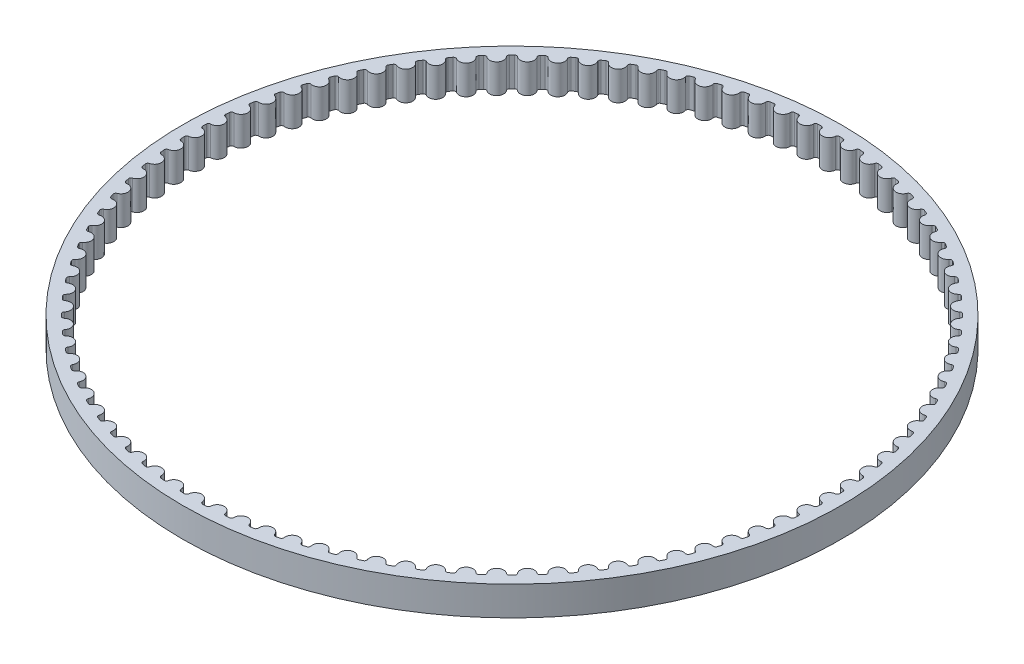
SolidWorks part; units mm, degrees
ref_plane "Front Plane" through (0, 0, 0) normal (0, 0, 1) x (1, 0, 0)
ref_plane "Top Plane" through (0, 0, 0) normal (0, 1, 0) x (1, 0, 0)
ref_plane "Right Plane" through (0, 0, 0) normal (1, 0, 0) x (0, 0, -1)
sketch "Sketch1" plane through (0, 0, 0) normal (0, 1, 0) x (1, 0, 0)
  circle A0 centre (0, 0) radius 45.0458
  arc B0 (-1.7256, -43.5116) -> (-1.2478, -43.5279) centre (0, 0) ccw
  arc B1 (-1.2478, -43.5279) -> (-0.9418, -43.2593) centre (-1.2392, -43.229) ccw
  arc B2 (0.9418, -43.2593) -> (-0.9418, -43.2593) centre (0, -43.3553) ccw
  arc B3 (0.9418, -43.2593) -> (1.2478, -43.5279) centre (1.2392, -43.229) ccw
  arc B4 (1.2478, -43.5279) -> (1.7256, -43.5116) centre (0, 0) ccw
  arc B5 (1.7256, -43.5116) -> (2.0125, -43.2227) centre (1.7137, -43.2128) ccw
  arc B6 (3.8917, -43.0942) -> (2.0125, -43.2227) centre (2.9587, -43.2542) ccw
  arc B7 (3.8917, -43.0942) -> (4.2153, -43.3413) centre (4.1864, -43.0437) ccw
  arc B8 (4.2153, -43.3413) -> (4.6909, -43.2924) centre (0, 0) ccw
  arc B9 (4.6909, -43.2924) -> (4.9575, -42.9846) centre (4.6587, -42.9951) ccw
  arc B10 (6.8235, -42.7282) -> (4.9575, -42.9846) centre (5.9035, -42.9515) ccw
  arc B11 (6.8235, -42.7282) -> (7.1632, -42.9526) centre (7.114, -42.6576) ccw
  arc B12 (7.1632, -42.9526) -> (7.6343, -42.8713) centre (0, 0) ccw
  arc B13 (7.6343, -42.8713) -> (7.8793, -42.5461) centre (7.5819, -42.577) ccw
  arc B14 (9.7234, -42.1629) -> (7.8793, -42.5461) centre (8.8209, -42.4484) ccw
  arc B15 (9.7234, -42.1629) -> (10.0777, -42.3636) centre (10.0085, -42.0727) ccw
  arc B16 (10.0777, -42.3636) -> (10.5422, -42.2504) centre (0, 0) ccw
  arc B17 (10.5422, -42.2504) -> (10.7644, -41.9092) centre (10.4698, -41.9603) ccw
  arc B18 (12.5781, -41.4011) -> (10.7644, -41.9092) centre (11.6971, -41.7475) ccw
  arc B19 (12.5781, -41.4011) -> (12.9452, -41.5771) centre (12.8563, -41.2916) ccw
  arc B20 (12.9452, -41.5771) -> (13.4008, -41.4325) centre (0, 0) ccw
  arc B21 (13.4008, -41.4325) -> (13.5993, -41.0769) centre (13.3088, -41.148) ccw
  arc B22 (15.3741, -40.4462) -> (13.5993, -41.0769) centre (14.5188, -40.852) ccw
  arc B23 (15.3741, -40.4462) -> (15.7524, -40.5968) centre (15.6442, -40.318) ccw
  arc B24 (15.7524, -40.5968) -> (16.1971, -40.4214) centre (0, 0) ccw
  arc B25 (16.1971, -40.4214) -> (16.3708, -40.0531) centre (16.0858, -40.1438) ccw
  arc B26 (18.0984, -39.3027) -> (16.3708, -40.0531) centre (17.2728, -39.7659) ccw
  arc B27 (18.0984, -39.3027) -> (18.4861, -39.4271) centre (18.3591, -39.1564) ccw
  arc B28 (18.4861, -39.4271) -> (18.9178, -39.2218) centre (0, 0) ccw
  arc B29 (18.9178, -39.2218) -> (19.0659, -38.8426) centre (18.7879, -38.9525) ccw
  arc B30 (20.7383, -37.976) -> (19.0659, -38.8426) centre (19.9462, -38.4945) ccw
  arc B31 (20.7383, -37.976) -> (21.1336, -38.0737) centre (20.9884, -37.8123) ccw
  arc B32 (21.1336, -38.0737) -> (21.5502, -37.8394) centre (0, 0) ccw
  arc B33 (21.5502, -37.8394) -> (21.6722, -37.4509) centre (21.4023, -37.5796) ccw
  arc B34 (23.2815, -36.4723) -> (21.6722, -37.4509) centre (22.5267, -37.0436) ccw
  arc B35 (23.2815, -36.4723) -> (23.6825, -36.5427) centre (23.5199, -36.2918) ccw
  arc B36 (23.6825, -36.5427) -> (24.0823, -36.2806) centre (0, 0) ccw
  arc B37 (24.0823, -36.2806) -> (24.1774, -35.8847) centre (23.9169, -36.0314) ccw
  arc B38 (25.7162, -34.7985) -> (24.1774, -35.8847) centre (25.0021, -35.4199) ccw
  arc B39 (25.7162, -34.7985) -> (26.1211, -34.8414) centre (25.9417, -34.6022) ccw
  arc B40 (26.1211, -34.8414) -> (26.502, -34.5525) centre (0, 0) ccw
  arc B41 (26.502, -34.5525) -> (26.5699, -34.1511) centre (26.32, -34.3153) ccw
  arc B42 (28.031, -32.9624) -> (26.5699, -34.1511) centre (27.361, -33.6312) ccw
  arc B43 (28.031, -32.9624) -> (28.4379, -32.9776) centre (28.2426, -32.7512) ccw
  arc B44 (28.4379, -32.9776) -> (28.7982, -32.6634) centre (0, 0) ccw
  arc B45 (28.7982, -32.6634) -> (28.8385, -32.2583) centre (28.6004, -32.4392) ccw
  arc B46 (30.2151, -30.9727) -> (28.8385, -32.2583) centre (29.5923, -31.6856) ccw
  arc B47 (30.2151, -30.9727) -> (30.622, -30.9601) centre (30.4118, -30.7475) ccw
  arc B48 (30.622, -30.9601) -> (30.9601, -30.622) centre (0, 0) ccw
  arc B49 (30.9601, -30.622) -> (30.9727, -30.2151) centre (30.7475, -30.4118) ccw
  arc B50 (32.2583, -28.8385) -> (30.9727, -30.2151) centre (31.6856, -29.5923) ccw
  arc B51 (32.2583, -28.8385) -> (32.6634, -28.7982) centre (32.4392, -28.6004) ccw
  arc B52 (32.6634, -28.7982) -> (32.9776, -28.4379) centre (0, 0) ccw
  arc B53 (32.9776, -28.4379) -> (32.9624, -28.031) centre (32.7512, -28.2426) ccw
  arc B54 (34.1511, -26.5699) -> (32.9624, -28.031) centre (33.6312, -27.361) ccw
  arc B55 (34.1511, -26.5699) -> (34.5525, -26.502) centre (34.3153, -26.32) ccw
  arc B56 (34.5525, -26.502) -> (34.8414, -26.1211) centre (0, 0) ccw
  arc B57 (34.8414, -26.1211) -> (34.7985, -25.7162) centre (34.6022, -25.9417) ccw
  arc B58 (35.8847, -24.1774) -> (34.7985, -25.7162) centre (35.4199, -25.0021) ccw
  arc B59 (35.8847, -24.1774) -> (36.2806, -24.0823) centre (36.0314, -23.9169) ccw
  arc B60 (36.2806, -24.0823) -> (36.5427, -23.6825) centre (0, 0) ccw
  arc B61 (36.5427, -23.6825) -> (36.4723, -23.2815) centre (36.2918, -23.5199) ccw
  arc B62 (37.4509, -21.6722) -> (36.4723, -23.2815) centre (37.0436, -22.5267) ccw
  arc B63 (37.4509, -21.6722) -> (37.8394, -21.5502) centre (37.5796, -21.4023) ccw
  arc B64 (37.8394, -21.5502) -> (38.0737, -21.1336) centre (0, 0) ccw
  arc B65 (38.0737, -21.1336) -> (37.976, -20.7383) centre (37.8123, -20.9884) ccw
  arc B66 (38.8426, -19.0659) -> (37.976, -20.7383) centre (38.4945, -19.9462) ccw
  arc B67 (38.8426, -19.0659) -> (39.2218, -18.9178) centre (38.9525, -18.7879) ccw
  arc B68 (39.2218, -18.9178) -> (39.4271, -18.4861) centre (0, 0) ccw
  arc B69 (39.4271, -18.4861) -> (39.3027, -18.0984) centre (39.1564, -18.3591) ccw
  arc B70 (40.0531, -16.3708) -> (39.3027, -18.0984) centre (39.7659, -17.2728) ccw
  arc B71 (40.0531, -16.3708) -> (40.4214, -16.1971) centre (40.1438, -16.0858) ccw
  arc B72 (40.4214, -16.1971) -> (40.5968, -15.7524) centre (0, 0) ccw
  arc B73 (40.5968, -15.7524) -> (40.4462, -15.3741) centre (40.318, -15.6442) ccw
  arc B74 (41.0769, -13.5993) -> (40.4462, -15.3741) centre (40.852, -14.5188) ccw
  arc B75 (41.0769, -13.5993) -> (41.4325, -13.4008) centre (41.148, -13.3088) ccw
  arc B76 (41.4325, -13.4008) -> (41.5771, -12.9452) centre (0, 0) ccw
  arc B77 (41.5771, -12.9452) -> (41.4011, -12.5781) centre (41.2916, -12.8563) ccw
  arc B78 (41.9092, -10.7644) -> (41.4011, -12.5781) centre (41.7475, -11.6971) ccw
  arc B79 (41.9092, -10.7644) -> (42.2504, -10.5422) centre (41.9603, -10.4698) ccw
  arc B80 (42.2504, -10.5422) -> (42.3636, -10.0777) centre (0, 0) ccw
  arc B81 (42.3636, -10.0777) -> (42.1629, -9.7234) centre (42.0727, -10.0085) ccw
  arc B82 (42.5461, -7.8793) -> (42.1629, -9.7234) centre (42.4484, -8.8209) ccw
  arc B83 (42.5461, -7.8793) -> (42.8713, -7.6343) centre (42.577, -7.5819) ccw
  arc B84 (42.8713, -7.6343) -> (42.9526, -7.1632) centre (0, 0) ccw
  arc B85 (42.9526, -7.1632) -> (42.7282, -6.8235) centre (42.6576, -7.114) ccw
  arc B86 (42.9846, -4.9575) -> (42.7282, -6.8235) centre (42.9515, -5.9035) ccw
  arc B87 (42.9846, -4.9575) -> (43.2924, -4.6909) centre (42.9951, -4.6587) ccw
  arc B88 (43.2924, -4.6909) -> (43.3413, -4.2153) centre (0, 0) ccw
  arc B89 (43.3413, -4.2153) -> (43.0942, -3.8917) centre (43.0437, -4.1864) ccw
  arc B90 (43.2227, -2.0125) -> (43.0942, -3.8917) centre (43.2542, -2.9587) ccw
  arc B91 (43.2227, -2.0125) -> (43.5116, -1.7256) centre (43.2128, -1.7137) ccw
  arc B92 (43.5116, -1.7256) -> (43.5279, -1.2478) centre (0, 0) ccw
  arc B93 (43.5279, -1.2478) -> (43.2593, -0.9418) centre (43.229, -1.2392) ccw
  arc B94 (43.2593, 0.9418) -> (43.2593, -0.9418) centre (43.3553, 0) ccw
  arc B95 (43.2593, 0.9418) -> (43.5279, 1.2478) centre (43.229, 1.2392) ccw
  arc B96 (43.5279, 1.2478) -> (43.5116, 1.7256) centre (0, 0) ccw
  arc B97 (43.5116, 1.7256) -> (43.2227, 2.0125) centre (43.2128, 1.7137) ccw
  arc B98 (43.0942, 3.8917) -> (43.2227, 2.0125) centre (43.2542, 2.9587) ccw
  arc B99 (43.0942, 3.8917) -> (43.3413, 4.2153) centre (43.0437, 4.1864) ccw
  arc B100 (43.3413, 4.2153) -> (43.2924, 4.6909) centre (0, 0) ccw
  arc B101 (43.2924, 4.6909) -> (42.9846, 4.9575) centre (42.9951, 4.6587) ccw
  arc B102 (42.7282, 6.8235) -> (42.9846, 4.9575) centre (42.9515, 5.9035) ccw
  arc B103 (42.7282, 6.8235) -> (42.9526, 7.1632) centre (42.6576, 7.114) ccw
  arc B104 (42.9526, 7.1632) -> (42.8713, 7.6343) centre (0, 0) ccw
  arc B105 (42.8713, 7.6343) -> (42.5461, 7.8793) centre (42.577, 7.5819) ccw
  arc B106 (42.1629, 9.7234) -> (42.5461, 7.8793) centre (42.4484, 8.8209) ccw
  arc B107 (42.1629, 9.7234) -> (42.3636, 10.0777) centre (42.0727, 10.0085) ccw
  arc B108 (42.3636, 10.0777) -> (42.2504, 10.5422) centre (0, 0) ccw
  arc B109 (42.2504, 10.5422) -> (41.9092, 10.7644) centre (41.9603, 10.4698) ccw
  arc B110 (41.4011, 12.5781) -> (41.9092, 10.7644) centre (41.7475, 11.6971) ccw
  arc B111 (41.4011, 12.5781) -> (41.5771, 12.9452) centre (41.2916, 12.8563) ccw
  arc B112 (41.5771, 12.9452) -> (41.4325, 13.4008) centre (0, 0) ccw
  arc B113 (41.4325, 13.4008) -> (41.0769, 13.5993) centre (41.148, 13.3088) ccw
  arc B114 (40.4462, 15.3741) -> (41.0769, 13.5993) centre (40.852, 14.5188) ccw
  arc B115 (40.4462, 15.3741) -> (40.5968, 15.7524) centre (40.318, 15.6442) ccw
  arc B116 (40.5968, 15.7524) -> (40.4214, 16.1971) centre (0, 0) ccw
  arc B117 (40.4214, 16.1971) -> (40.0531, 16.3708) centre (40.1438, 16.0858) ccw
  arc B118 (39.3027, 18.0984) -> (40.0531, 16.3708) centre (39.7659, 17.2728) ccw
  arc B119 (39.3027, 18.0984) -> (39.4271, 18.4861) centre (39.1564, 18.3591) ccw
  arc B120 (39.4271, 18.4861) -> (39.2218, 18.9178) centre (0, 0) ccw
  arc B121 (39.2218, 18.9178) -> (38.8426, 19.0659) centre (38.9525, 18.7879) ccw
  arc B122 (37.976, 20.7383) -> (38.8426, 19.0659) centre (38.4945, 19.9462) ccw
  arc B123 (37.976, 20.7383) -> (38.0737, 21.1336) centre (37.8123, 20.9884) ccw
  arc B124 (38.0737, 21.1336) -> (37.8394, 21.5502) centre (0, 0) ccw
  arc B125 (37.8394, 21.5502) -> (37.4509, 21.6722) centre (37.5796, 21.4023) ccw
  arc B126 (36.4723, 23.2815) -> (37.4509, 21.6722) centre (37.0436, 22.5267) ccw
  arc B127 (36.4723, 23.2815) -> (36.5427, 23.6825) centre (36.2918, 23.5199) ccw
  arc B128 (36.5427, 23.6825) -> (36.2806, 24.0823) centre (0, 0) ccw
  arc B129 (36.2806, 24.0823) -> (35.8847, 24.1774) centre (36.0314, 23.9169) ccw
  arc B130 (34.7985, 25.7162) -> (35.8847, 24.1774) centre (35.4199, 25.0021) ccw
  arc B131 (34.7985, 25.7162) -> (34.8414, 26.1211) centre (34.6022, 25.9417) ccw
  arc B132 (34.8414, 26.1211) -> (34.5525, 26.502) centre (0, 0) ccw
  arc B133 (34.5525, 26.502) -> (34.1511, 26.5699) centre (34.3153, 26.32) ccw
  arc B134 (32.9624, 28.031) -> (34.1511, 26.5699) centre (33.6312, 27.361) ccw
  arc B135 (32.9624, 28.031) -> (32.9776, 28.4379) centre (32.7512, 28.2426) ccw
  arc B136 (32.9776, 28.4379) -> (32.6634, 28.7982) centre (0, 0) ccw
  arc B137 (32.6634, 28.7982) -> (32.2583, 28.8385) centre (32.4392, 28.6004) ccw
  arc B138 (30.9727, 30.2151) -> (32.2583, 28.8385) centre (31.6856, 29.5923) ccw
  arc B139 (30.9727, 30.2151) -> (30.9601, 30.622) centre (30.7475, 30.4118) ccw
  arc B140 (30.9601, 30.622) -> (30.622, 30.9601) centre (0, 0) ccw
  arc B141 (30.622, 30.9601) -> (30.2151, 30.9727) centre (30.4118, 30.7475) ccw
  arc B142 (28.8385, 32.2583) -> (30.2151, 30.9727) centre (29.5923, 31.6856) ccw
  arc B143 (28.8385, 32.2583) -> (28.7982, 32.6634) centre (28.6004, 32.4392) ccw
  arc B144 (28.7982, 32.6634) -> (28.4379, 32.9776) centre (0, 0) ccw
  arc B145 (28.4379, 32.9776) -> (28.031, 32.9624) centre (28.2426, 32.7512) ccw
  arc B146 (26.5699, 34.1511) -> (28.031, 32.9624) centre (27.361, 33.6312) ccw
  arc B147 (26.5699, 34.1511) -> (26.502, 34.5525) centre (26.32, 34.3153) ccw
  arc B148 (26.502, 34.5525) -> (26.1211, 34.8414) centre (0, 0) ccw
  arc B149 (26.1211, 34.8414) -> (25.7162, 34.7985) centre (25.9417, 34.6022) ccw
  arc B150 (24.1774, 35.8847) -> (25.7162, 34.7985) centre (25.0021, 35.4199) ccw
  arc B151 (24.1774, 35.8847) -> (24.0823, 36.2806) centre (23.9169, 36.0314) ccw
  arc B152 (24.0823, 36.2806) -> (23.6825, 36.5427) centre (0, 0) ccw
  arc B153 (23.6825, 36.5427) -> (23.2815, 36.4723) centre (23.5199, 36.2918) ccw
  arc B154 (21.6722, 37.4509) -> (23.2815, 36.4723) centre (22.5267, 37.0436) ccw
  arc B155 (21.6722, 37.4509) -> (21.5502, 37.8394) centre (21.4023, 37.5796) ccw
  arc B156 (21.5502, 37.8394) -> (21.1336, 38.0737) centre (0, 0) ccw
  arc B157 (21.1336, 38.0737) -> (20.7383, 37.976) centre (20.9884, 37.8123) ccw
  arc B158 (19.0659, 38.8426) -> (20.7383, 37.976) centre (19.9462, 38.4945) ccw
  arc B159 (19.0659, 38.8426) -> (18.9178, 39.2218) centre (18.7879, 38.9525) ccw
  arc B160 (18.9178, 39.2218) -> (18.4861, 39.4271) centre (0, 0) ccw
  arc B161 (18.4861, 39.4271) -> (18.0984, 39.3027) centre (18.3591, 39.1564) ccw
  arc B162 (16.3708, 40.0531) -> (18.0984, 39.3027) centre (17.2728, 39.7659) ccw
  arc B163 (16.3708, 40.0531) -> (16.1971, 40.4214) centre (16.0858, 40.1438) ccw
  arc B164 (16.1971, 40.4214) -> (15.7524, 40.5968) centre (0, 0) ccw
  arc B165 (15.7524, 40.5968) -> (15.3741, 40.4462) centre (15.6442, 40.318) ccw
  arc B166 (13.5993, 41.0769) -> (15.3741, 40.4462) centre (14.5188, 40.852) ccw
  arc B167 (13.5993, 41.0769) -> (13.4008, 41.4325) centre (13.3088, 41.148) ccw
  arc B168 (13.4008, 41.4325) -> (12.9452, 41.5771) centre (0, 0) ccw
  arc B169 (12.9452, 41.5771) -> (12.5781, 41.4011) centre (12.8563, 41.2916) ccw
  arc B170 (10.7644, 41.9092) -> (12.5781, 41.4011) centre (11.6971, 41.7475) ccw
  arc B171 (10.7644, 41.9092) -> (10.5422, 42.2504) centre (10.4698, 41.9603) ccw
  arc B172 (10.5422, 42.2504) -> (10.0777, 42.3636) centre (0, 0) ccw
  arc B173 (10.0777, 42.3636) -> (9.7234, 42.1629) centre (10.0085, 42.0727) ccw
  arc B174 (7.8793, 42.5461) -> (9.7234, 42.1629) centre (8.8209, 42.4484) ccw
  arc B175 (7.8793, 42.5461) -> (7.6343, 42.8713) centre (7.5819, 42.577) ccw
  arc B176 (7.6343, 42.8713) -> (7.1632, 42.9526) centre (0, 0) ccw
  arc B177 (7.1632, 42.9526) -> (6.8235, 42.7282) centre (7.114, 42.6576) ccw
  arc B178 (4.9575, 42.9846) -> (6.8235, 42.7282) centre (5.9035, 42.9515) ccw
  arc B179 (4.9575, 42.9846) -> (4.6909, 43.2924) centre (4.6587, 42.9951) ccw
  arc B180 (4.6909, 43.2924) -> (4.2153, 43.3413) centre (0, 0) ccw
  arc B181 (4.2153, 43.3413) -> (3.8917, 43.0942) centre (4.1864, 43.0437) ccw
  arc B182 (2.0125, 43.2227) -> (3.8917, 43.0942) centre (2.9587, 43.2542) ccw
  arc B183 (2.0125, 43.2227) -> (1.7256, 43.5116) centre (1.7137, 43.2128) ccw
  arc B184 (1.7256, 43.5116) -> (1.2478, 43.5279) centre (0, 0) ccw
  arc B185 (1.2478, 43.5279) -> (0.9418, 43.2593) centre (1.2392, 43.229) ccw
  arc B186 (-0.9418, 43.2593) -> (0.9418, 43.2593) centre (0, 43.3553) ccw
  arc B187 (-0.9418, 43.2593) -> (-1.2478, 43.5279) centre (-1.2392, 43.229) ccw
  arc B188 (-1.2478, 43.5279) -> (-1.7256, 43.5116) centre (0, 0) ccw
  arc B189 (-1.7256, 43.5116) -> (-2.0125, 43.2227) centre (-1.7137, 43.2128) ccw
  arc B190 (-3.8917, 43.0942) -> (-2.0125, 43.2227) centre (-2.9587, 43.2542) ccw
  arc B191 (-3.8917, 43.0942) -> (-4.2153, 43.3413) centre (-4.1864, 43.0437) ccw
  arc B192 (-4.2153, 43.3413) -> (-4.6909, 43.2924) centre (0, 0) ccw
  arc B193 (-4.6909, 43.2924) -> (-4.9575, 42.9846) centre (-4.6587, 42.9951) ccw
  arc B194 (-6.8235, 42.7282) -> (-4.9575, 42.9846) centre (-5.9035, 42.9515) ccw
  arc B195 (-6.8235, 42.7282) -> (-7.1632, 42.9526) centre (-7.114, 42.6576) ccw
  arc B196 (-7.1632, 42.9526) -> (-7.6343, 42.8713) centre (0, 0) ccw
  arc B197 (-7.6343, 42.8713) -> (-7.8793, 42.5461) centre (-7.5819, 42.577) ccw
  arc B198 (-9.7234, 42.1629) -> (-7.8793, 42.5461) centre (-8.8209, 42.4484) ccw
  arc B199 (-9.7234, 42.1629) -> (-10.0777, 42.3636) centre (-10.0085, 42.0727) ccw
  arc B200 (-10.0777, 42.3636) -> (-10.5422, 42.2504) centre (0, 0) ccw
  arc B201 (-10.5422, 42.2504) -> (-10.7644, 41.9092) centre (-10.4698, 41.9603) ccw
  arc B202 (-12.5781, 41.4011) -> (-10.7644, 41.9092) centre (-11.6971, 41.7475) ccw
  arc B203 (-12.5781, 41.4011) -> (-12.9452, 41.5771) centre (-12.8563, 41.2916) ccw
  arc B204 (-12.9452, 41.5771) -> (-13.4008, 41.4325) centre (0, 0) ccw
  arc B205 (-13.4008, 41.4325) -> (-13.5993, 41.0769) centre (-13.3088, 41.148) ccw
  arc B206 (-15.3741, 40.4462) -> (-13.5993, 41.0769) centre (-14.5188, 40.852) ccw
  arc B207 (-15.3741, 40.4462) -> (-15.7524, 40.5968) centre (-15.6442, 40.318) ccw
  arc B208 (-15.7524, 40.5968) -> (-16.1971, 40.4214) centre (0, 0) ccw
  arc B209 (-16.1971, 40.4214) -> (-16.3708, 40.0531) centre (-16.0858, 40.1438) ccw
  arc B210 (-18.0984, 39.3027) -> (-16.3708, 40.0531) centre (-17.2728, 39.7659) ccw
  arc B211 (-18.0984, 39.3027) -> (-18.4861, 39.4271) centre (-18.3591, 39.1564) ccw
  arc B212 (-18.4861, 39.4271) -> (-18.9178, 39.2218) centre (0, 0) ccw
  arc B213 (-18.9178, 39.2218) -> (-19.0659, 38.8426) centre (-18.7879, 38.9525) ccw
  arc B214 (-20.7383, 37.976) -> (-19.0659, 38.8426) centre (-19.9462, 38.4945) ccw
  arc B215 (-20.7383, 37.976) -> (-21.1336, 38.0737) centre (-20.9884, 37.8123) ccw
  arc B216 (-21.1336, 38.0737) -> (-21.5502, 37.8394) centre (0, 0) ccw
  arc B217 (-21.5502, 37.8394) -> (-21.6722, 37.4509) centre (-21.4023, 37.5796) ccw
  arc B218 (-23.2815, 36.4723) -> (-21.6722, 37.4509) centre (-22.5267, 37.0436) ccw
  arc B219 (-23.2815, 36.4723) -> (-23.6825, 36.5427) centre (-23.5199, 36.2918) ccw
  arc B220 (-23.6825, 36.5427) -> (-24.0823, 36.2806) centre (0, 0) ccw
  arc B221 (-24.0823, 36.2806) -> (-24.1774, 35.8847) centre (-23.9169, 36.0314) ccw
  arc B222 (-25.7162, 34.7985) -> (-24.1774, 35.8847) centre (-25.0021, 35.4199) ccw
  arc B223 (-25.7162, 34.7985) -> (-26.1211, 34.8414) centre (-25.9417, 34.6022) ccw
  arc B224 (-26.1211, 34.8414) -> (-26.502, 34.5525) centre (0, 0) ccw
  arc B225 (-26.502, 34.5525) -> (-26.5699, 34.1511) centre (-26.32, 34.3153) ccw
  arc B226 (-28.031, 32.9624) -> (-26.5699, 34.1511) centre (-27.361, 33.6312) ccw
  arc B227 (-28.031, 32.9624) -> (-28.4379, 32.9776) centre (-28.2426, 32.7512) ccw
  arc B228 (-28.4379, 32.9776) -> (-28.7982, 32.6634) centre (0, 0) ccw
  arc B229 (-28.7982, 32.6634) -> (-28.8385, 32.2583) centre (-28.6004, 32.4392) ccw
  arc B230 (-30.2151, 30.9727) -> (-28.8385, 32.2583) centre (-29.5923, 31.6856) ccw
  arc B231 (-30.2151, 30.9727) -> (-30.622, 30.9601) centre (-30.4118, 30.7475) ccw
  arc B232 (-30.622, 30.9601) -> (-30.9601, 30.622) centre (0, 0) ccw
  arc B233 (-30.9601, 30.622) -> (-30.9727, 30.2151) centre (-30.7475, 30.4118) ccw
  arc B234 (-32.2583, 28.8385) -> (-30.9727, 30.2151) centre (-31.6856, 29.5923) ccw
  arc B235 (-32.2583, 28.8385) -> (-32.6634, 28.7982) centre (-32.4392, 28.6004) ccw
  arc B236 (-32.6634, 28.7982) -> (-32.9776, 28.4379) centre (0, 0) ccw
  arc B237 (-32.9776, 28.4379) -> (-32.9624, 28.031) centre (-32.7512, 28.2426) ccw
  arc B238 (-34.1511, 26.5699) -> (-32.9624, 28.031) centre (-33.6312, 27.361) ccw
  arc B239 (-34.1511, 26.5699) -> (-34.5525, 26.502) centre (-34.3153, 26.32) ccw
  arc B240 (-34.5525, 26.502) -> (-34.8414, 26.1211) centre (0, 0) ccw
  arc B241 (-34.8414, 26.1211) -> (-34.7985, 25.7162) centre (-34.6022, 25.9417) ccw
  arc B242 (-35.8847, 24.1774) -> (-34.7985, 25.7162) centre (-35.4199, 25.0021) ccw
  arc B243 (-35.8847, 24.1774) -> (-36.2806, 24.0823) centre (-36.0314, 23.9169) ccw
  arc B244 (-36.2806, 24.0823) -> (-36.5427, 23.6825) centre (0, 0) ccw
  arc B245 (-36.5427, 23.6825) -> (-36.4723, 23.2815) centre (-36.2918, 23.5199) ccw
  arc B246 (-37.4509, 21.6722) -> (-36.4723, 23.2815) centre (-37.0436, 22.5267) ccw
  arc B247 (-37.4509, 21.6722) -> (-37.8394, 21.5502) centre (-37.5796, 21.4023) ccw
  arc B248 (-37.8394, 21.5502) -> (-38.0737, 21.1336) centre (0, 0) ccw
  arc B249 (-38.0737, 21.1336) -> (-37.976, 20.7383) centre (-37.8123, 20.9884) ccw
  arc B250 (-38.8426, 19.0659) -> (-37.976, 20.7383) centre (-38.4945, 19.9462) ccw
  arc B251 (-38.8426, 19.0659) -> (-39.2218, 18.9178) centre (-38.9525, 18.7879) ccw
  arc B252 (-39.2218, 18.9178) -> (-39.4271, 18.4861) centre (0, 0) ccw
  arc B253 (-39.4271, 18.4861) -> (-39.3027, 18.0984) centre (-39.1564, 18.3591) ccw
  arc B254 (-40.0531, 16.3708) -> (-39.3027, 18.0984) centre (-39.7659, 17.2728) ccw
  arc B255 (-40.0531, 16.3708) -> (-40.4214, 16.1971) centre (-40.1438, 16.0858) ccw
  arc B256 (-40.4214, 16.1971) -> (-40.5968, 15.7524) centre (0, 0) ccw
  arc B257 (-40.5968, 15.7524) -> (-40.4462, 15.3741) centre (-40.318, 15.6442) ccw
  arc B258 (-41.0769, 13.5993) -> (-40.4462, 15.3741) centre (-40.852, 14.5188) ccw
  arc B259 (-41.0769, 13.5993) -> (-41.4325, 13.4008) centre (-41.148, 13.3088) ccw
  arc B260 (-41.4325, 13.4008) -> (-41.5771, 12.9452) centre (0, 0) ccw
  arc B261 (-41.5771, 12.9452) -> (-41.4011, 12.5781) centre (-41.2916, 12.8563) ccw
  arc B262 (-41.9092, 10.7644) -> (-41.4011, 12.5781) centre (-41.7475, 11.6971) ccw
  arc B263 (-41.9092, 10.7644) -> (-42.2504, 10.5422) centre (-41.9603, 10.4698) ccw
  arc B264 (-42.2504, 10.5422) -> (-42.3636, 10.0777) centre (0, 0) ccw
  arc B265 (-42.3636, 10.0777) -> (-42.1629, 9.7234) centre (-42.0727, 10.0085) ccw
  arc B266 (-42.5461, 7.8793) -> (-42.1629, 9.7234) centre (-42.4484, 8.8209) ccw
  arc B267 (-42.5461, 7.8793) -> (-42.8713, 7.6343) centre (-42.577, 7.5819) ccw
  arc B268 (-42.8713, 7.6343) -> (-42.9526, 7.1632) centre (0, 0) ccw
  arc B269 (-42.9526, 7.1632) -> (-42.7282, 6.8235) centre (-42.6576, 7.114) ccw
  arc B270 (-42.9846, 4.9575) -> (-42.7282, 6.8235) centre (-42.9515, 5.9035) ccw
  arc B271 (-42.9846, 4.9575) -> (-43.2924, 4.6909) centre (-42.9951, 4.6587) ccw
  arc B272 (-43.2924, 4.6909) -> (-43.3413, 4.2153) centre (0, 0) ccw
  arc B273 (-43.3413, 4.2153) -> (-43.0942, 3.8917) centre (-43.0437, 4.1864) ccw
  arc B274 (-43.2227, 2.0125) -> (-43.0942, 3.8917) centre (-43.2542, 2.9587) ccw
  arc B275 (-43.2227, 2.0125) -> (-43.5116, 1.7256) centre (-43.2128, 1.7137) ccw
  arc B276 (-43.5116, 1.7256) -> (-43.5279, 1.2478) centre (0, 0) ccw
  arc B277 (-43.5279, 1.2478) -> (-43.2593, 0.9418) centre (-43.229, 1.2392) ccw
  arc B278 (-43.2593, -0.9418) -> (-43.2593, 0.9418) centre (-43.3553, 0) ccw
  arc B279 (-43.2593, -0.9418) -> (-43.5279, -1.2478) centre (-43.229, -1.2392) ccw
  arc B280 (-43.5279, -1.2478) -> (-43.5116, -1.7256) centre (0, 0) ccw
  arc B281 (-43.5116, -1.7256) -> (-43.2227, -2.0125) centre (-43.2128, -1.7137) ccw
  arc B282 (-43.0942, -3.8917) -> (-43.2227, -2.0125) centre (-43.2542, -2.9587) ccw
  arc B283 (-43.0942, -3.8917) -> (-43.3413, -4.2153) centre (-43.0437, -4.1864) ccw
  arc B284 (-43.3413, -4.2153) -> (-43.2924, -4.6909) centre (0, 0) ccw
  arc B285 (-43.2924, -4.6909) -> (-42.9846, -4.9575) centre (-42.9951, -4.6587) ccw
  arc B286 (-42.7282, -6.8235) -> (-42.9846, -4.9575) centre (-42.9515, -5.9035) ccw
  arc B287 (-42.7282, -6.8235) -> (-42.9526, -7.1632) centre (-42.6576, -7.114) ccw
  arc B288 (-42.9526, -7.1632) -> (-42.8713, -7.6343) centre (0, 0) ccw
  arc B289 (-42.8713, -7.6343) -> (-42.5461, -7.8793) centre (-42.577, -7.5819) ccw
  arc B290 (-42.1629, -9.7234) -> (-42.5461, -7.8793) centre (-42.4484, -8.8209) ccw
  arc B291 (-42.1629, -9.7234) -> (-42.3636, -10.0777) centre (-42.0727, -10.0085) ccw
  arc B292 (-42.3636, -10.0777) -> (-42.2504, -10.5422) centre (0, 0) ccw
  arc B293 (-42.2504, -10.5422) -> (-41.9092, -10.7644) centre (-41.9603, -10.4698) ccw
  arc B294 (-41.4011, -12.5781) -> (-41.9092, -10.7644) centre (-41.7475, -11.6971) ccw
  arc B295 (-41.4011, -12.5781) -> (-41.5771, -12.9452) centre (-41.2916, -12.8563) ccw
  arc B296 (-41.5771, -12.9452) -> (-41.4325, -13.4008) centre (0, 0) ccw
  arc B297 (-41.4325, -13.4008) -> (-41.0769, -13.5993) centre (-41.148, -13.3088) ccw
  arc B298 (-40.4462, -15.3741) -> (-41.0769, -13.5993) centre (-40.852, -14.5188) ccw
  arc B299 (-40.4462, -15.3741) -> (-40.5968, -15.7524) centre (-40.318, -15.6442) ccw
  arc B300 (-40.5968, -15.7524) -> (-40.4214, -16.1971) centre (0, 0) ccw
  arc B301 (-40.4214, -16.1971) -> (-40.0531, -16.3708) centre (-40.1438, -16.0858) ccw
  arc B302 (-39.3027, -18.0984) -> (-40.0531, -16.3708) centre (-39.7659, -17.2728) ccw
  arc B303 (-39.3027, -18.0984) -> (-39.4271, -18.4861) centre (-39.1564, -18.3591) ccw
  arc B304 (-39.4271, -18.4861) -> (-39.2218, -18.9178) centre (0, 0) ccw
  arc B305 (-39.2218, -18.9178) -> (-38.8426, -19.0659) centre (-38.9525, -18.7879) ccw
  arc B306 (-37.976, -20.7383) -> (-38.8426, -19.0659) centre (-38.4945, -19.9462) ccw
  arc B307 (-37.976, -20.7383) -> (-38.0737, -21.1336) centre (-37.8123, -20.9884) ccw
  arc B308 (-38.0737, -21.1336) -> (-37.8394, -21.5502) centre (0, 0) ccw
  arc B309 (-37.8394, -21.5502) -> (-37.4509, -21.6722) centre (-37.5796, -21.4023) ccw
  arc B310 (-36.4723, -23.2815) -> (-37.4509, -21.6722) centre (-37.0436, -22.5267) ccw
  arc B311 (-36.4723, -23.2815) -> (-36.5427, -23.6825) centre (-36.2918, -23.5199) ccw
  arc B312 (-36.5427, -23.6825) -> (-36.2806, -24.0823) centre (0, 0) ccw
  arc B313 (-36.2806, -24.0823) -> (-35.8847, -24.1774) centre (-36.0314, -23.9169) ccw
  arc B314 (-34.7985, -25.7162) -> (-35.8847, -24.1774) centre (-35.4199, -25.0021) ccw
  arc B315 (-34.7985, -25.7162) -> (-34.8414, -26.1211) centre (-34.6022, -25.9417) ccw
  arc B316 (-34.8414, -26.1211) -> (-34.5525, -26.502) centre (0, 0) ccw
  arc B317 (-34.5525, -26.502) -> (-34.1511, -26.5699) centre (-34.3153, -26.32) ccw
  arc B318 (-32.9624, -28.031) -> (-34.1511, -26.5699) centre (-33.6312, -27.361) ccw
  arc B319 (-32.9624, -28.031) -> (-32.9776, -28.4379) centre (-32.7512, -28.2426) ccw
  arc B320 (-32.9776, -28.4379) -> (-32.6634, -28.7982) centre (0, 0) ccw
  arc B321 (-32.6634, -28.7982) -> (-32.2583, -28.8385) centre (-32.4392, -28.6004) ccw
  arc B322 (-30.9727, -30.2151) -> (-32.2583, -28.8385) centre (-31.6856, -29.5923) ccw
  arc B323 (-30.9727, -30.2151) -> (-30.9601, -30.622) centre (-30.7475, -30.4118) ccw
  arc B324 (-30.9601, -30.622) -> (-30.622, -30.9601) centre (0, 0) ccw
  arc B325 (-30.622, -30.9601) -> (-30.2151, -30.9727) centre (-30.4118, -30.7475) ccw
  arc B326 (-28.8385, -32.2583) -> (-30.2151, -30.9727) centre (-29.5923, -31.6856) ccw
  arc B327 (-28.8385, -32.2583) -> (-28.7982, -32.6634) centre (-28.6004, -32.4392) ccw
  arc B328 (-28.7982, -32.6634) -> (-28.4379, -32.9776) centre (0, 0) ccw
  arc B329 (-28.4379, -32.9776) -> (-28.031, -32.9624) centre (-28.2426, -32.7512) ccw
  arc B330 (-26.5699, -34.1511) -> (-28.031, -32.9624) centre (-27.361, -33.6312) ccw
  arc B331 (-26.5699, -34.1511) -> (-26.502, -34.5525) centre (-26.32, -34.3153) ccw
  arc B332 (-26.502, -34.5525) -> (-26.1211, -34.8414) centre (0, 0) ccw
  arc B333 (-26.1211, -34.8414) -> (-25.7162, -34.7985) centre (-25.9417, -34.6022) ccw
  arc B334 (-24.1774, -35.8847) -> (-25.7162, -34.7985) centre (-25.0021, -35.4199) ccw
  arc B335 (-24.1774, -35.8847) -> (-24.0823, -36.2806) centre (-23.9169, -36.0314) ccw
  arc B336 (-24.0823, -36.2806) -> (-23.6825, -36.5427) centre (0, 0) ccw
  arc B337 (-23.6825, -36.5427) -> (-23.2815, -36.4723) centre (-23.5199, -36.2918) ccw
  arc B338 (-21.6722, -37.4509) -> (-23.2815, -36.4723) centre (-22.5267, -37.0436) ccw
  arc B339 (-21.6722, -37.4509) -> (-21.5502, -37.8394) centre (-21.4023, -37.5796) ccw
  arc B340 (-21.5502, -37.8394) -> (-21.1336, -38.0737) centre (0, 0) ccw
  arc B341 (-21.1336, -38.0737) -> (-20.7383, -37.976) centre (-20.9884, -37.8123) ccw
  arc B342 (-19.0659, -38.8426) -> (-20.7383, -37.976) centre (-19.9462, -38.4945) ccw
  arc B343 (-19.0659, -38.8426) -> (-18.9178, -39.2218) centre (-18.7879, -38.9525) ccw
  arc B344 (-18.9178, -39.2218) -> (-18.4861, -39.4271) centre (0, 0) ccw
  arc B345 (-18.4861, -39.4271) -> (-18.0984, -39.3027) centre (-18.3591, -39.1564) ccw
  arc B346 (-16.3708, -40.0531) -> (-18.0984, -39.3027) centre (-17.2728, -39.7659) ccw
  arc B347 (-16.3708, -40.0531) -> (-16.1971, -40.4214) centre (-16.0858, -40.1438) ccw
  arc B348 (-16.1971, -40.4214) -> (-15.7524, -40.5968) centre (0, 0) ccw
  arc B349 (-15.7524, -40.5968) -> (-15.3741, -40.4462) centre (-15.6442, -40.318) ccw
  arc B350 (-13.5993, -41.0769) -> (-15.3741, -40.4462) centre (-14.5188, -40.852) ccw
  arc B351 (-13.5993, -41.0769) -> (-13.4008, -41.4325) centre (-13.3088, -41.148) ccw
  arc B352 (-13.4008, -41.4325) -> (-12.9452, -41.5771) centre (0, 0) ccw
  arc B353 (-12.9452, -41.5771) -> (-12.5781, -41.4011) centre (-12.8563, -41.2916) ccw
  arc B354 (-10.7644, -41.9092) -> (-12.5781, -41.4011) centre (-11.6971, -41.7475) ccw
  arc B355 (-10.7644, -41.9092) -> (-10.5422, -42.2504) centre (-10.4698, -41.9603) ccw
  arc B356 (-10.5422, -42.2504) -> (-10.0777, -42.3636) centre (0, 0) ccw
  arc B357 (-10.0777, -42.3636) -> (-9.7234, -42.1629) centre (-10.0085, -42.0727) ccw
  arc B358 (-7.8793, -42.5461) -> (-9.7234, -42.1629) centre (-8.8209, -42.4484) ccw
  arc B359 (-7.8793, -42.5461) -> (-7.6343, -42.8713) centre (-7.5819, -42.577) ccw
  arc B360 (-7.6343, -42.8713) -> (-7.1632, -42.9526) centre (0, 0) ccw
  arc B361 (-7.1632, -42.9526) -> (-6.8235, -42.7282) centre (-7.114, -42.6576) ccw
  arc B362 (-4.9575, -42.9846) -> (-6.8235, -42.7282) centre (-5.9035, -42.9515) ccw
  arc B363 (-4.9575, -42.9846) -> (-4.6909, -43.2924) centre (-4.6587, -42.9951) ccw
  arc B364 (-4.6909, -43.2924) -> (-4.2153, -43.3413) centre (0, 0) ccw
  arc B365 (-4.2153, -43.3413) -> (-3.8917, -43.0942) centre (-4.1864, -43.0437) ccw
  arc B366 (-2.0125, -43.2227) -> (-3.8917, -43.0942) centre (-2.9587, -43.2542) ccw
  arc B367 (-2.0125, -43.2227) -> (-1.7256, -43.5116) centre (-1.7137, -43.2128) ccw
  dimension "D1" = 1.5
sketch_block_instance "Block-92T GT2 Pulley-1"
sketch_block "Block-92T GT2 Pulley"
extrude "Boss-Extrude1" add sketch "Sketch1" along normal blind 4
